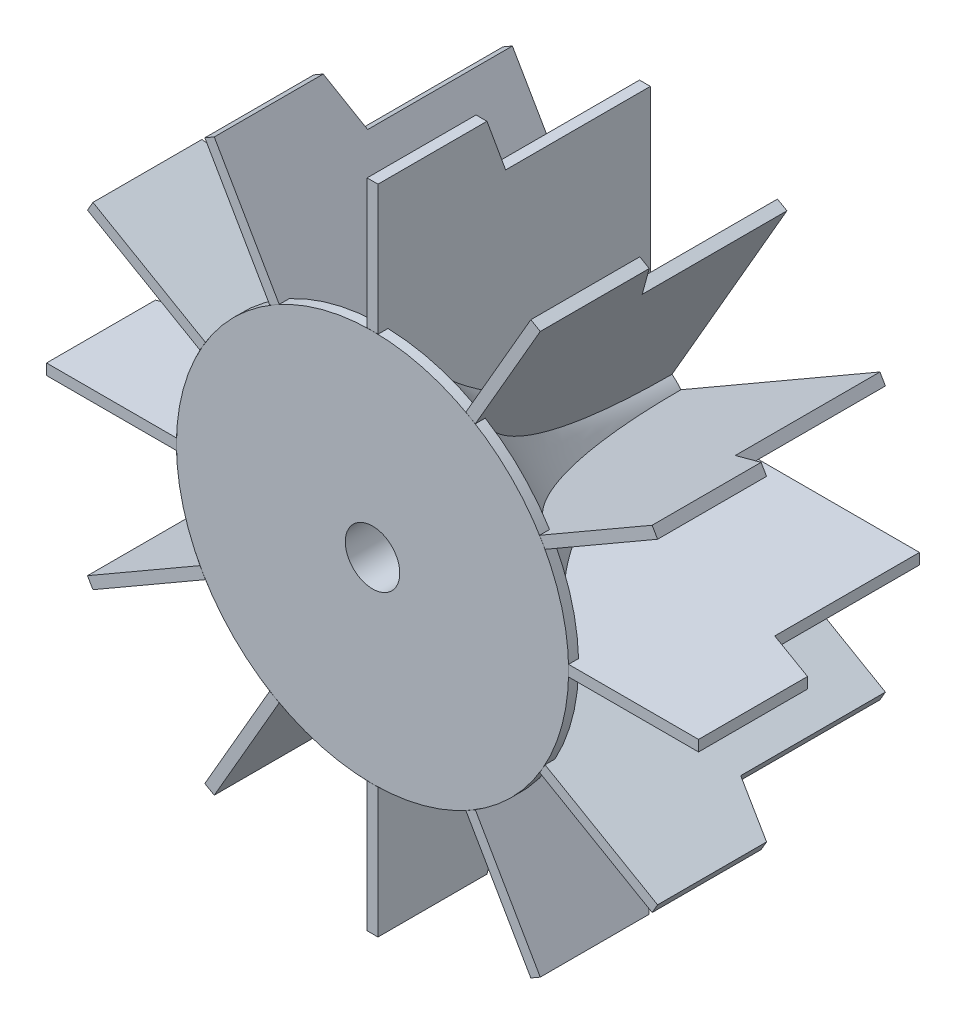
SolidWorks part; units mm, degrees
ref_plane "Front Plane" through (0, 0, 0) normal (0, 0, 1) x (1, 0, 0)
ref_plane "Top Plane" through (0, 0, 0) normal (0, 1, 0) x (1, 0, 0)
ref_plane "Right Plane" through (0, 0, 0) normal (1, 0, 0) x (0, 0, -1)
sketch "Sketch1" plane through (0, 0, 0) normal (0, 1, 0) x (1, 0, 0)
  line L0 (0, 0) -> (22.86, 0)
  line L1 (22.86, 0) -> (22.86, 1.1619)
  line L2 (5.2453, 31.75) -> (0, 31.75)
  line L3 (0, 31.75) -> (0, 0)
  line L4 (5.2453, 31.75) -> (5.2453, 39.3668) construction
  arc A0 (22.86, 1.1619) -> (5.2453, 31.75) centre (40.6109, 31.75) cw
  point P6 (25.4, 0)
  point P8 (25.4, 5.7439)
  point P10 (6.35, 25.4)
  point P11 (0, 0)
  point P12 (0, 0)
  point P13 (0, 0)
  point P14 (6.35, 33.0168)
  point P15 (6.35, 25.4)
  point P16 (0, 0)
  point P17 (6.2937, 25.4)
  point P18 (25.4, 0)
  point P19 (6.7095, 25.4)
  point P20 (0, 0)
  point P21 (23.0376, 0)
  point P22 (22.86, 1.1619)
  dimension "D1" = 22.86
  dimension "D3" = 31.75
revolve "Revolve1" add sketch "Sketch1" angle 360 about L3
sketch "Sketch2" plane through (0, 0, -31.75) normal (0, 0, -1) x (-1, 0, 0)
  circle A0 centre (0, 0) radius 3.175
  dimension "D1" = 6.35
extrude "Cut-Extrude1" cut sketch "Sketch2" against normal through all
sketch "Sketch4" plane through (0, 0, 0) normal (1, 0, 0) x (0, 0, -1)
  line L0 (31.75, -5.2453) -> (31.75, 5.2453) construction
  line L1 (0, 22.86) -> (0, -22.86) construction
  line L2 (0, 0) -> (46.2649, 0) construction
  line L3 (0, -38) -> (0, -22.86)
  line L4 (0, -22.86) -> (4.4965, -6.2004)
  line L5 (4.4965, -6.2004) -> (31.75, -4.782)
  line L6 (31.75, -4.782) -> (31.75, -32)
  line L7 (0, 22.86) -> (0, -22.86) construction
  line L8 (0, -38) -> (12.7, -38)
  line L9 (12.7, -38) -> (14.8838, -32)
  line L10 (14.8838, -32) -> (31.75, -32)
  point P1 (25.4, -32)
  point P17 (5.248, -38)
  point P18 (0, 0)
  point P19 (0, 0)
  point P20 (0, 0)
  point P21 (5.4985, -25.4042)
  point P22 (0, -22.86)
  point P23 (7.3354, -9.0392)
  point P24 (4.4965, -6.2004)
  point P25 (15.3148, -32)
  dimension "D1" = 38
  dimension "D2" = 32
  dimension "D3" = 12.7
  dimension "D4" = 70
extrude "Boss-Extrude1" add sketch "Sketch4" along normal mid plane 1.27
pattern_circular "CirPattern1" count 12 over 360 about axis through (0, 0, 0) along (0, 0, 1) of "Boss-Extrude1"
